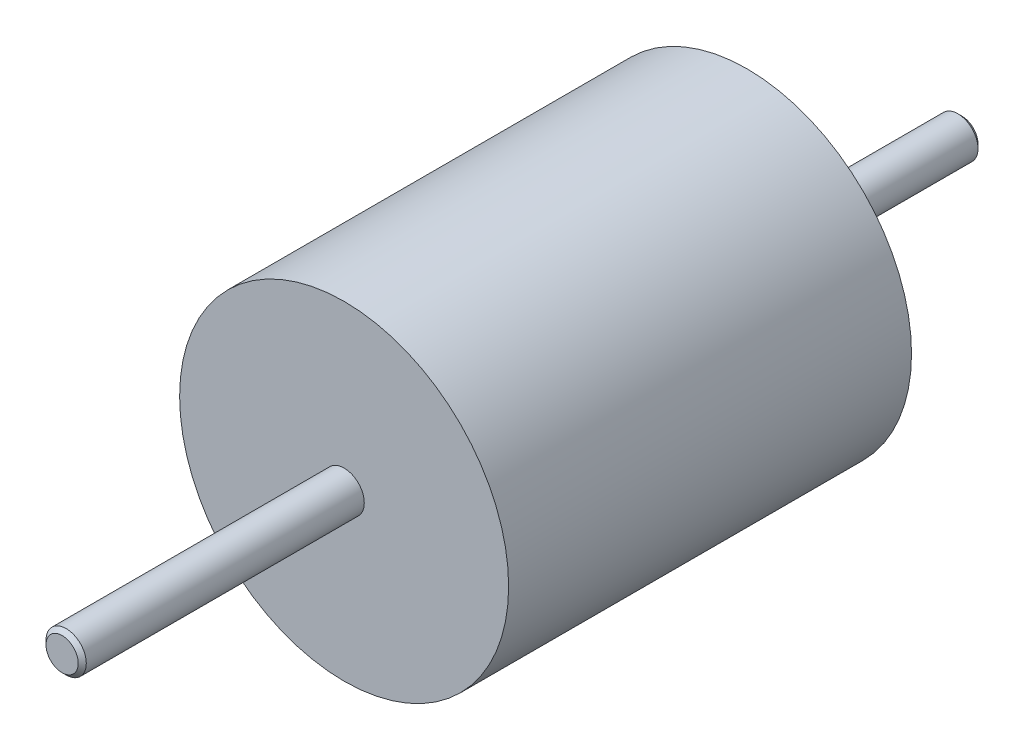
SolidWorks part; units mm, degrees
ref_plane "Front Plane" through (0, 0, 0) normal (0, 0, 1) x (1, 0, 0)
ref_plane "Top Plane" through (0, 0, 0) normal (0, 1, 0) x (1, 0, 0)
ref_plane "Right Plane" through (0, 0, 0) normal (1, 0, 0) x (0, 0, -1)
sketch "Sketch1" plane through (0, 0, 0) normal (0, 0, 1) x (1, 0, 0)
  circle A0 centre (0, 0) radius 1.5
  dimension "D1" = 3
extrude "Boss-Extrude1" add sketch "Sketch1" along normal mid plane 67
ref_plane "Plane1" through (0, 0, 12.5) normal (0, 0, 1) x (1, 0, 0)
sketch "Sketch2" plane through (0, 0, 12.5) normal (0, 0, 1) x (1, 0, 0)
  circle A0 centre (0, 0) radius 1.5 construction
  circle A1 centre (0, 0) radius 1.5
  circle A2 centre (0, 0) radius 12.25
  dimension "D1" = 24.5
extrude "Boss-Extrude2" add sketch "Sketch2" against normal blind 30
chamfer "Chamfer1" distance 0.3 angle 45 2 edges at (1.5, 0, -33.5) (1.5, 0, 33.5)
